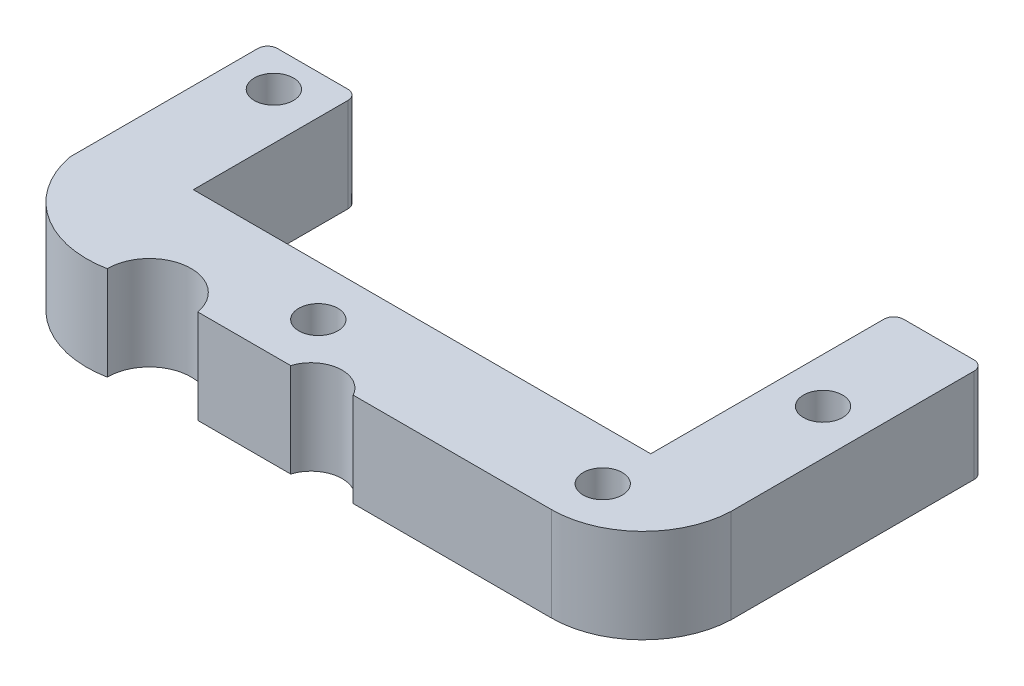
SolidWorks part; units mm, degrees
ref_plane "Front Plane" through (0, 0, 0) normal (0, 0, 1) x (1, 0, 0)
ref_plane "Top Plane" through (0, 0, 0) normal (0, 1, 0) x (1, 0, 0)
ref_plane "Right Plane" through (0, 0, 0) normal (1, 0, 0) x (0, 0, -1)
sketch "Sketch1" plane through (0, 0, 0) normal (0, 1, 0) x (1, 0, 0)
  line L0 (-10.7302, 4.1433) -> (629.2698, 4.1433) construction
  line L1 (0, 0) -> (0, 10.11)
  line L10 (0, 0) -> (0, 10.11)
  line L11 (4.6, 1.7142) -> (27.9674, 1.7142)
  line L12 (27.9674, 14.1261) -> (32.5674, 14.1261)
  line L13 (0, 10.11) -> (4.6, 10.11)
  line L14 (32.5674, 14.1261) -> (32.5674, 1.2241)
  line L15 (27.9674, 1.7142) -> (27.9674, 14.1261)
  line L16 (4.6, 10.11) -> (4.6, 1.7142)
  line L17 (27.9002, -3.2903) -> (17.7701, -3.2903)
  line L18 (10.1218, -3.5807) -> (14.8689, -3.5807)
  arc A8 (32.5674, 1.2241) -> (27.9002, -3.2903) centre (27.8909, 1.3892) cw
  arc A9 (0, 0) -> (5.8973, -3.9784) centre (4.9379, 0.9595) ccw
  circle A10 centre (28.0679, -0.8397) radius 1
  arc A11 (14.8689, -3.5807) -> (17.7701, -3.2903) centre (16.3811, -4.0512) cw
  arc A12 (5.8973, -3.9784) -> (10.1218, -3.5807) centre (8.0262, -3.9558) cw
  circle A13 centre (30.2674, 8.2158) radius 1
  circle A14 centre (2.213, 8.2158) radius 1
  circle A15 centre (13.5393, -0.8397) radius 1
  point P3 (2.3, 10.11)
  point P5 (30.2674, 14.1261)
  point P10 (0, 0)
  dimension "D1" = 2
  dimension "D3" = 2
  dimension "D4" = 2
  dimension "D5" = 2
  dimension "D2" = 23.3674
  dimension "D6" = 4.6
  dimension "D7" = 4.6
extrude "Boss-Extrude1" add sketch "Sketch1" along normal blind 4.8 contours L0 L1 A9 A12 L18 A11 L17 A8 L14 L15 L11 L16 A15 A10 | L15 L0 L14 L12 A13 | L10 L0 L16 L13 A14
fillet "Fillet1" radius 0.5 4 edges at (32.5674, 2.4, -14.1261) (27.9674, 2.4, -14.1261) (4.6, 2.4, -10.11) (0, 2.4, -10.11)
